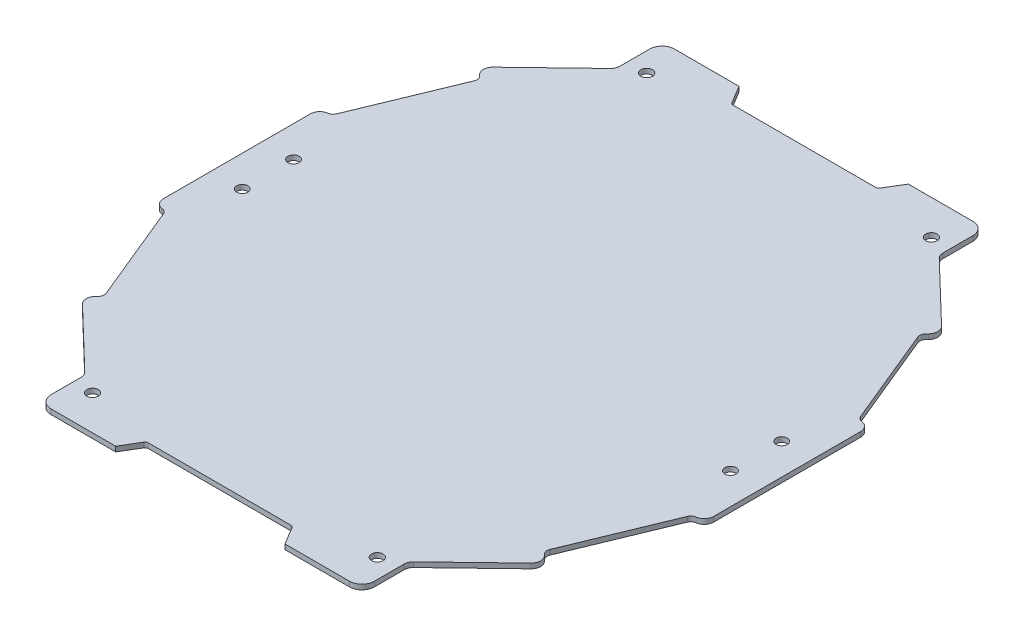
SolidWorks part; units mm, degrees
ref_plane "Front Plane" through (0, 0, 0) normal (0, 0, 1) x (1, 0, 0)
ref_plane "Top Plane" through (0, 0, 0) normal (0, 1, 0) x (1, 0, 0)
ref_plane "Right Plane" through (0, 0, 0) normal (1, 0, 0) x (0, 0, -1)
ref_plane "Plane1"
sketch "Sketch1" plane through (0, 0, 0) normal (0, 1, 0) x (-1, 0, 0)
  line L0 (74.0875, 321.0883) -> (70.3692, 327.2855)
  line L1 (70.3692, 327.2855) -> (45.5805, 327.2855)
  line L2 (45.5805, 327.2855) -> (45.5805, 312.4122)
  line L3 (45.5805, 312.4122) -> (23.246, 290.9343)
  line L4 (23.246, 290.9343) -> (26.6825, 287.3608)
  line L5 (26.6825, 287.3608) -> (12.7354, 253.539)
  line L6 (12.7354, 253.539) -> (9.0171, 253.539)
  line L7 (9.0171, 253.539) -> (9.0171, 226.8911)
  line L8 (9.0171, 226.8911) -> (9.0171, 200.2432)
  line L9 (9.0171, 200.2432) -> (12.7354, 200.2432)
  line L10 (12.7354, 200.2432) -> (26.6825, 166.4214)
  line L11 (26.6825, 166.4214) -> (23.246, 162.8479)
  line L12 (23.246, 162.8479) -> (45.5805, 141.37)
  line L13 (45.5805, 141.37) -> (45.5805, 126.4967)
  line L14 (45.5805, 126.4967) -> (70.3692, 126.4967)
  line L15 (70.3692, 126.4967) -> (74.0875, 132.6939)
  line L16 (74.0875, 132.6939) -> (97.6368, 132.6939)
  line L17 (97.6368, 132.6939) -> (121.1861, 132.6939)
  line L18 (121.1861, 132.6939) -> (124.9044, 126.4967)
  line L19 (124.9044, 126.4967) -> (149.6932, 126.4967)
  line L20 (149.6932, 126.4967) -> (149.6932, 141.37)
  line L21 (149.6932, 141.37) -> (172.0276, 162.8479)
  line L22 (172.0276, 162.8479) -> (168.5911, 166.4214)
  line L23 (168.5911, 166.4214) -> (182.5382, 200.2432)
  line L24 (182.5382, 200.2432) -> (186.2565, 200.2432)
  line L25 (186.2565, 200.2432) -> (186.2565, 226.8911)
  line L26 (186.2565, 226.8911) -> (186.2565, 253.539)
  line L27 (186.2565, 253.539) -> (182.5382, 253.539)
  line L28 (182.5382, 253.539) -> (168.5911, 287.3608)
  line L29 (168.5911, 287.3608) -> (172.0276, 290.9343)
  line L30 (172.0276, 290.9343) -> (149.6932, 312.4122)
  line L31 (149.6932, 312.4122) -> (149.6932, 327.2855)
  line L32 (149.6932, 327.2855) -> (124.9044, 327.2855)
  line L33 (124.9044, 327.2855) -> (121.1861, 321.0883)
  line L34 (121.1861, 321.0883) -> (97.6368, 321.0883)
  line L35 (97.6368, 321.0883) -> (74.0875, 321.0883)
  line L36 (97.6368, 132.6939) -> (97.6368, 321.0883) construction
  line L37 (9.0171, 226.8911) -> (186.2565, 226.8911) construction
  line L126 (176.3908, 226.8911) -> (176.3908, 225.1916)
  circle A8 centre (176.2565, 218.6411) radius 1.8
  circle A9 centre (176.2565, 235.1411) radius 1.8
  circle A10 centre (19.0171, 218.6411) radius 1.8
  circle A11 centre (19.0171, 235.1411) radius 1.8
  circle A22 centre (51.7777, 316.1305) radius 1.8592
  circle A27 centre (143.496, 137.6517) radius 1.8592
  circle A30 centre (143.496, 316.1305) radius 1.8592
  circle A77 centre (51.7777, 137.6517) radius 1.8592
  dimension "D28" = 6.1972
  dimension "D29" = 10
  dimension "D30" = 16.5
  dimension "D31" = 8.25
extrude "Extrusion1" add sketch "Sketch1" along normal blind 1.6
fillet "Fillet1" radius 1 4 edges at (-121.1861, 0.8, 132.6939) (-74.0875, 0.8, 132.6939) (-74.0875, 0.8, 321.0883) (-121.1861, 0.8, 321.0883)
fillet "Fillet2" radius 4 4 edges at (-149.6932, 0.8, 126.4967) (-45.5805, 0.8, 126.4967) (-149.6932, 0.8, 327.2855) (-45.5805, 0.8, 327.2855)
fillet "Fillet3" radius 3 4 edges at (-149.6932, 0.8, 141.37) (-45.5805, 0.8, 141.37) (-45.5805, 0.8, 312.4122) (-149.6932, 0.8, 312.4122)
fillet "Fillet4" radius 3 1 edges at (-172.0276, 0.8, 290.9343)
fillet "Fillet5" radius 2 1 edges at (-168.5911, 0.8, 287.3608)
fillet "Fillet6" radius 2 1 edges at (-26.6825, 0.8, 287.3608)
fillet "Fillet7" radius 3 1 edges at (-23.246, 0.8, 290.9343)
fillet "Fillet8" radius 3 2 edges at (-172.0276, 0.8, 162.8479) (-23.246, 0.8, 162.8479)
fillet "Fillet9" radius 2 2 edges at (-26.6825, 0.8, 166.4214) (-168.5911, 0.8, 166.4214)
fillet "Fillet10" radius 2 4 edges at (-12.7354, 0.8, 200.2432) (-12.7354, 0.8, 253.539) (-182.5382, 0.8, 253.539) (-182.5382, 0.8, 200.2432)
fillet "Fillet11" radius 3 4 edges at (-186.2565, 0.8, 200.2432) (-186.2565, 0.8, 253.539) (-9.0171, 0.8, 253.539) (-9.0171, 0.8, 200.2432)
